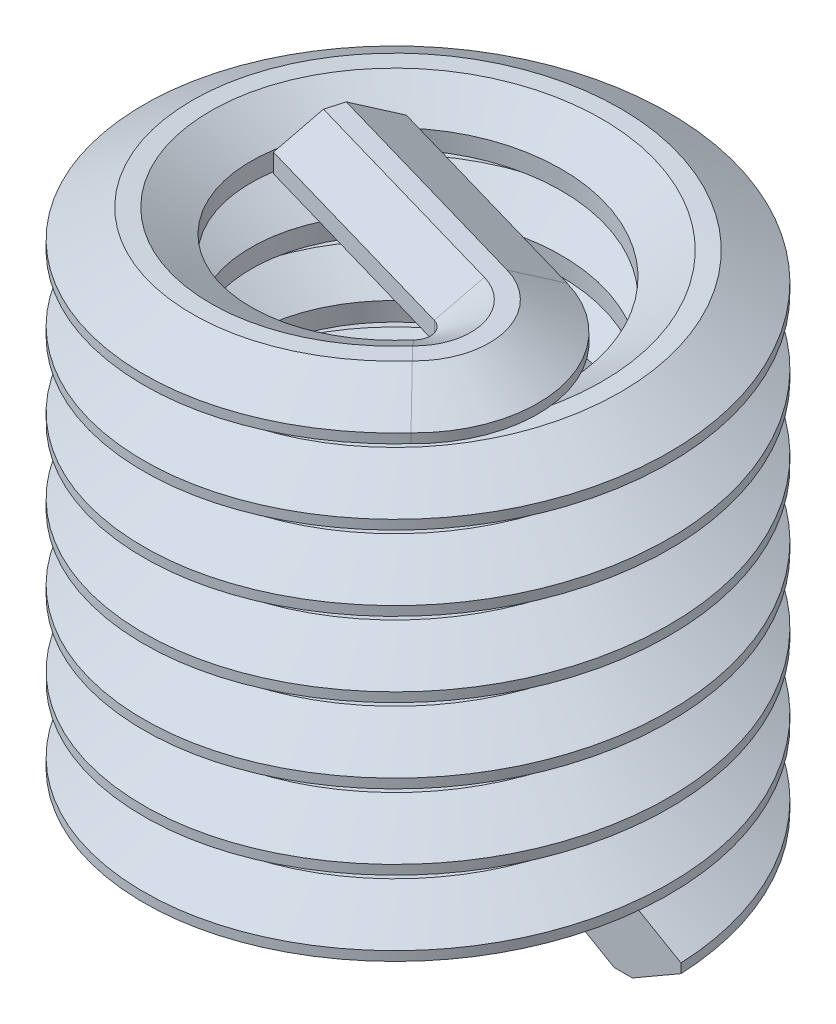
SolidWorks part; units mm, degrees
ref_plane "Front Plane" through (0, 0, 0) normal (0, 0, 1) x (1, 0, 0)
ref_plane "Top Plane" through (0, 0, 0) normal (0, 1, 0) x (1, 0, 0)
ref_plane "Right Plane" through (0, 0, 0) normal (1, 0, 0) x (0, 0, -1)
sketch "Sketch1" plane through (0, 0, 0) normal (0, 0, 1) x (-1, 0, 0)
  line L0 (0, 0) -> (0, 9.525) construction
  line L1 (-1.4813, 0) -> (-2.1687, 0.3969) construction
  line L2 (-2.1925, 0.3969) -> (-2.8799, 0) construction
  line L3 (-2.8799, 0) -> (-2.1925, -0.3969) construction
  line L4 (-2.1687, -0.3969) -> (-1.4813, 0) construction
  line L5 (-2.1687, -0.3969) -> (-2.1687, 0.3969) construction
  line L6 (-1.4813, 0) -> (0, 0) construction
  line L8 (-2.794, -0.0496) -> (-2.2784, -0.3473)
  line L9 (-2.0828, -0.3473) -> (-1.6532, -0.0992)
  line L10 (-1.5672, -0.0496) -> (-1.5672, 0.0496) construction
  line L11 (-1.6532, 0.0992) -> (-2.0828, 0.3473)
  line L12 (-2.2784, 0.3473) -> (-2.794, 0.0496)
  line L13 (-1.4813, 0) -> (-1.5672, 0) construction
  line L14 (-1.5672, 0) -> (-2.0828, 0) construction
  line L15 (-2.2784, 0) -> (-2.794, 0) construction
  line L16 (-2.794, 0) -> (-2.8799, 0) construction
  line L17 (-2.2784, 0.3473) -> (-2.0828, 0.3473)
  line L18 (-2.0828, 0.3473) -> (-2.0828, -0.3473) construction
  line L19 (-2.0828, -0.3473) -> (-2.2784, -0.3473)
  line L20 (-2.2784, -0.3473) -> (-2.2784, 0.3473) construction
  line L21 (-2.2784, 0) -> (-2.1687, 0) construction
  line L22 (-2.1687, 0) -> (-2.0828, 0) construction
  line L23 (-2.794, 0.3969) -> (-2.794, -5.8515) construction
  line L24 (-1.6532, -0.0992) -> (-1.6532, 0.0992)
  line L25 (-1.6532, 0) -> (-1.5672, 0) construction
  line L26 (-2.794, -0.0496) -> (-2.794, 0.0496)
  line L28 (2.794, 0.3969) -> (2.794, -5.8515) construction
  line L29 (-2.1687, -0.3969) -> (-2.1925, -0.3969) construction
  line L31 (-2.1925, 0.3969) -> (-2.1687, 0.3969) construction
  dimension "D3" = 0.7937
  dimension "D4" = 0.0992
  dimension "Installed Length" = 6.2484
  dimension "Thread Size" = 4.1656
  dimension "Max OD" = 5.588
sketch "Sketch2" plane through (0, 0, 0) normal (0, 1, 0) x (1, 0, 0)
  circle A0 centre (0, 0) radius 2.0828
curve "Helix/Spiral1" pitch 0.7937 height 5.4546 turns 6.872 parameters "Height"=5.4546, "Pitch"=0.7937
sweep "Sweep1" add profiles "Sketch1" path "Helix/Spiral1"
sketch "Sketch3" plane through (0, 0, 0) normal (0.7203, 0, -0.6936) x (-0.6936, 0, -0.7203)
  line L0 (-6.4046, 2.6123) -> (-1.4813, 5.4548) construction
  line L1 (-7.7298, 9.0624) -> (-1.4813, 5.4548) construction
  line L2 (-1.4813, 5.4548) -> (-1.4813, 5.6532) construction
  line L8 (-2.0828, 5.1075) -> (-1.6532, 5.3555)
  line L9 (-1.6532, 5.3555) -> (-1.6532, 5.554)
  line L10 (-1.6532, 5.554) -> (-2.0828, 5.802)
  line L12 (-2.2784, 5.802) -> (-2.794, 5.5044)
  line L13 (-2.794, 5.5044) -> (-2.794, 5.4052)
  line L14 (-2.794, 5.4052) -> (-2.2784, 5.1075)
  line L16 (-2.0828, 5.1075) -> (-1.6532, 5.3555)
  line L17 (-1.6532, 5.3555) -> (-1.6532, 5.554)
  line L18 (-1.6532, 5.554) -> (-2.0828, 5.802)
  line L20 (-2.2784, 5.802) -> (-2.794, 5.5044)
  line L21 (-2.794, 5.5044) -> (-2.794, 5.4052)
  line L22 (-2.794, 5.4052) -> (-2.2784, 5.1075)
  line L23 (-2.0828, 5.802) -> (-2.2784, 5.802)
  line L24 (-2.0828, 5.802) -> (-2.2784, 5.802)
  line L25 (-2.2784, 5.1075) -> (-2.0828, 5.1075)
  line L26 (-2.2784, 5.1075) -> (-2.0828, 5.1075)
  dimension "D1" = 0
revolve "Revolve1" add sketch "Sketch3" angle 120 about L2
sketch "Sketch4" plane through (1.2327, 0, 0.3553) normal (-0.9609, 0, -0.277) x (-0.277, 0, 0.9609)
  line L8 (-0.0565, 5.1075) -> (0.1392, 5.1075)
  line L9 (0.1392, 5.1075) -> (0.5688, 5.3555)
  line L10 (0.5688, 5.3555) -> (0.5688, 5.554)
  line L11 (0.5688, 5.554) -> (0.1392, 5.802)
  line L12 (-0.0565, 5.1075) -> (0.1392, 5.1075)
  line L13 (-0.0565, 5.802) -> (-0.572, 5.5044)
  line L14 (-0.572, 5.5044) -> (-0.572, 5.4052)
  line L15 (-0.572, 5.4052) -> (-0.0565, 5.1075)
  line L17 (0.1392, 5.1075) -> (0.5688, 5.3555)
  line L18 (0.5688, 5.3555) -> (0.5688, 5.554)
  line L19 (0.5688, 5.554) -> (0.1392, 5.802)
  line L21 (-0.0565, 5.802) -> (-0.572, 5.5044)
  line L22 (-0.572, 5.5044) -> (-0.572, 5.4052)
  line L23 (-0.572, 5.4052) -> (-0.0565, 5.1075)
  spline S4 degree 1 poles (2000.1282, 5.8009) (-2000.0472, 5.8031) knots -10222.580168 -10222.580168 10223.588828 10223.588828 only from (0.1392, 5.802) to (-0.0565, 5.802)
  spline S5 degree 1 poles (0.1392, 5.802) (-0.0565, 5.802) knots 0 0 1 1
  dimension "D1" = 0
extrude "Extrude1" add sketch "Sketch4" along normal blind 2.4994
sketch "Sketch5" plane through (0, 0, 0) normal (0, 1, 0) x (1, 0, 0)
  circle A0 centre (0, 0) radius 3.2033
equation "\"D3@Sketch1\" = \"Pitch@Helix/Spiral1\""
equation "\"D4@Sketch1\" = \"D3@Sketch1\"  * 1 / 8"
equation "\"D1@Extrude1\" = \"Thread Size@Sketch1\" * 0.6"
equation "\"Height@Helix/Spiral1\" = \"Installed Length@Sketch1\" - \"Pitch@Helix/Spiral1\""
